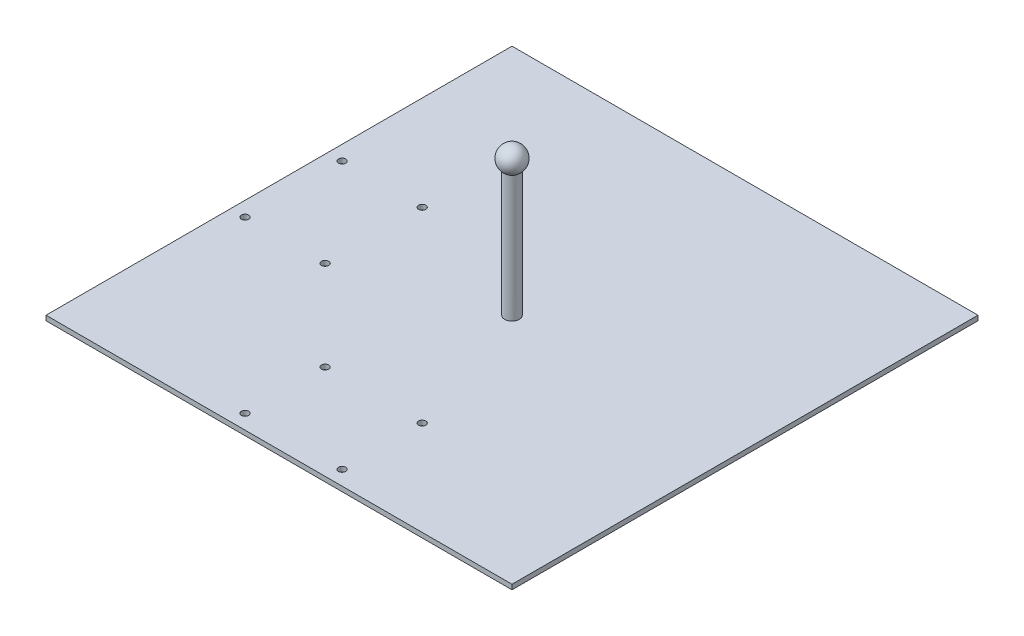
SolidWorks part; units mm, degrees
material "6061-T6 (SS)"
ref_plane "Front Plane" through (0, 0, 0) normal (0, 0, 1) x (1, 0, 0)
ref_plane "Top Plane" through (0, 0, 0) normal (0, 1, 0) x (1, 0, 0)
ref_plane "Right Plane" through (0, 0, 0) normal (1, 0, 0) x (0, 0, -1)
sketch "Sketch1" plane through (0, 0, 0) normal (0, 1, 0) x (1, 0, 0)
  line L1 (-304.8, -304.8) -> (304.8, -304.8)
  line L2 (-304.8, -304.8) -> (-304.8, 304.8)
  line L3 (-304.8, 304.8) -> (304.8, 304.8)
  line L4 (304.8, -304.8) -> (304.8, 304.8)
  dimension "D1" = 609.6
  dimension "D2" = 609.6
  dimension "D3" = 304.8
  dimension "D4" = 304.8
extrude "Boss-Extrude1" add sketch "Sketch1" along normal blind 6.35 contours L2 L3 L4 L1
hole_wizard "3/8 (0.375) Diameter Hole1" positions "Sketch2" profile "Sketch3" hole size "3/8" standard "ANSI Inch"
sketch "Sketch2" plane through (0, 6.35, 0) normal (0, 1, 0) x (1, 0, 0)
  line L1 (-304.8, -304.8) -> (-304.8, 304.8) construction
  line L3 (-304.8, -304.8) -> (304.8, -304.8) construction
  point P0 (-63.5, -285.75)
  point P2 (63.5, -285.75)
  point P4 (-285.75, 63.5)
  point P6 (-285.75, -63.5)
  point P17 (-304.8, 0)
  point P33 (-63.5, -180.975)
  point P35 (63.5, -180.975)
  point P37 (-180.975, -63.5)
  point P39 (-180.975, 63.5)
  dimension "D1" = 63.5
  dimension "D2" = 127
  dimension "D3" = 19.05
  dimension "D4" = 19.05
  dimension "D5" = 127
  dimension "D6" = 63.5
  dimension "D7" = 104.775
  dimension "D8" = 104.775
sketch "Sketch3" plane through (-63.5, 6.35, 285.75) normal (1, 0, 0) x (0, 0, 1)
  line L0 (0, 0) -> (0, 14.5456)
  line L1 (0, 14.5456) -> (4.7625, 11.684)
  line L2 (4.7625, 11.684) -> (4.7625, 0)
  line L5 (4.7625, 0) -> (0, 0)
  line L10 (0, 14.5456) -> (-4.7625, 11.684) construction
  line L11 (0, -6.35) -> (0, 107.95) construction
  dimension "Hole Dia." = 9.525
  dimension "Hole Depth" = 11.684
  dimension "Drill Angle" = 118
sketch "Sketch4" plane through (0, 6.35, 0) normal (0, 1, 0) x (1, 0, 0)
  circle A0 centre (0, 0) radius 9.525
  dimension "D1" = 19.05
extrude "Boss-Extrude2" add sketch "Sketch4" along normal blind 165.1
ref_axis "Axis1" through (0, 599.8237, 0) along (0, -1, 0)
sketch "Sketch5" plane through (0, 0, 0) normal (0, 0, 1) x (1, 0, 0)
  line L0 (0, 200.025) -> (0, 168.275)
  arc A0 (0, 200.025) -> (0, 168.275) centre (0, 184.15) ccw
  dimension "D1" = 31.75
revolve "Revolve3" add sketch "Sketch5" angle 360 about axis through (0, 599.8237, 0) along (0, -1, 0)
